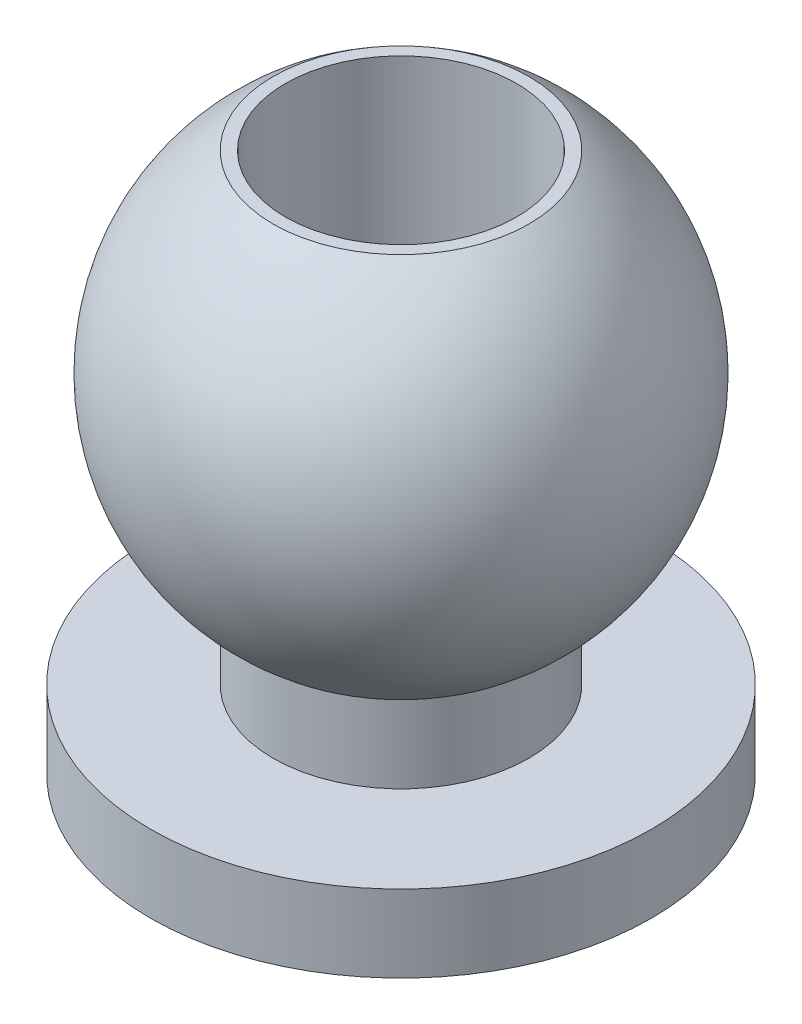
SolidWorks part; units mm, degrees
material "Brass"
ref_plane "Front Plane" through (0, 0, 0) normal (0, 0, 1) x (1, 0, 0)
ref_plane "Top Plane" through (0, 0, 0) normal (0, 1, 0) x (1, 0, 0)
ref_plane "Right Plane" through (0, 0, 0) normal (1, 0, 0) x (0, 0, -1)
sketch "Sketch1" plane through (0, 0, 0) normal (0, 0, 1) x (1, 0, 0)
  line L0 (0, 0) -> (0, 15.0444) construction
  line L1 (0, 0) -> (-3.25, 0)
  line L2 (-3.25, 0) -> (-3.25, 1)
  line L3 (-3.25, 1) -> (-1.6583, 1)
  line L4 (-1.6583, 1) -> (-1.6583, 2)
  line L5 (-1.6583, 7) -> (0, 7)
  line L8 (0, 7) -> (0, 0)
  arc A0 (-1.6583, 7) -> (-1.6583, 2) centre (0, 4.5) ccw
  point P4 (0, 4.5)
  point P5 (-1.6583, 7)
  point P6 (-1.6583, 2)
  dimension "D1" = 6
  dimension "D2" = 5
  dimension "D3" = 1
  dimension "D4" = 1
  dimension "D5" = 3.25
  dimension "D6" = 4.5
revolve "Revolve1" add sketch "Sketch1" angle 360 about L0
sketch "Sketch2" plane through (0, 7, 0) normal (0, 1, 0) x (1, 0, 0)
  circle A0 centre (0, 0) radius 1.5
  dimension "D1" = 3
extrude "Cut-Extrude1" cut sketch "Sketch2" against normal through all
sketch3d "3DSketch1" plane through (0, 0, 0) normal (0, 0, 1) x (1, 0, 0)
  dimension "D1" = 4.5
sketch3d "3DSketch2"
  point P0 (0, 4.5, 0)
